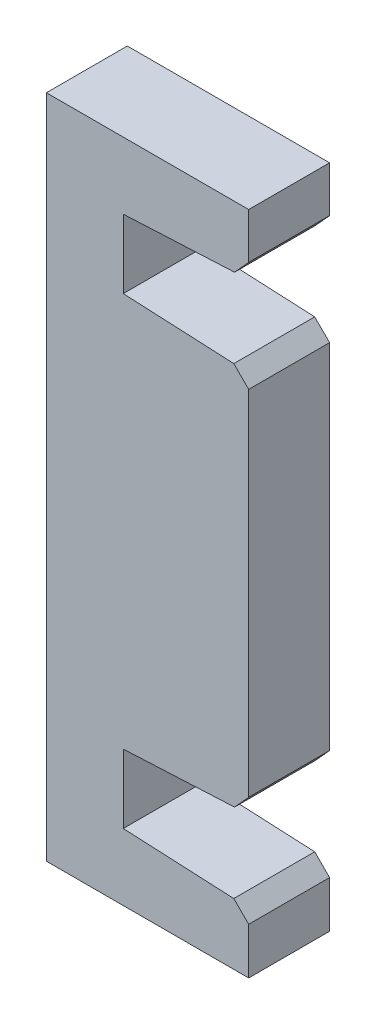
SolidWorks part; units mm, degrees
material "Oak"
ref_plane "Front Plane" through (0, 0, 0) normal (0, 0, 1) x (1, 0, 0)
ref_plane "Top Plane" through (0, 0, 0) normal (0, 1, 0) x (1, 0, 0)
ref_plane "Right Plane" through (0, 0, 0) normal (1, 0, 0) x (0, 0, -1)
sketch "Sketch1" plane through (0, 0, 0) normal (0, 0, 1) x (1, 0, 0)
  line L0 (0, -9.45) -> (0, 9.45)
  line L1 (0, 9.45) -> (-6.2, 9.75)
  line L2 (-6.2, 9.75) -> (-6.2, 13.15)
  line L3 (-6.2, 13.15) -> (0, 13.45)
  line L4 (0, 13.45) -> (0, 16.45)
  line L5 (0, 16.45) -> (-10, 16.45)
  line L6 (-10, 16.45) -> (-10, -16.45)
  line L7 (-10, 0) -> (0, 0)
  line L8 (-20.8617, 0) -> (22.0865, 0) construction
  line L9 (0, -16.45) -> (-10, -16.45)
  line L10 (0, -13.45) -> (0, -16.45)
  line L11 (-6.2, -13.15) -> (0, -13.45)
  line L12 (-6.2, -9.75) -> (-6.2, -13.15)
  line L13 (0, -9.45) -> (-6.2, -9.75)
  dimension "D1" = 4
  dimension "D2" = 3.4
  dimension "D3" = 19.5
  dimension "D4" = 3.8
  dimension "D5" = 10
  dimension "D6" = 3
extrude "Boss-Extrude1" add sketch "Sketch1" along normal blind 4 contours L6 L7 L0 L1 L2 L3 L4 L5 | L13 L0 L7 L6 L9 L10 L11 L12
chamfer "Chamfer1" distance 0.7 angle 45 4 edges at (0, -9.45, 2) (0, -13.45, 2) (0, 9.45, 2) (0, 13.45, 2)
